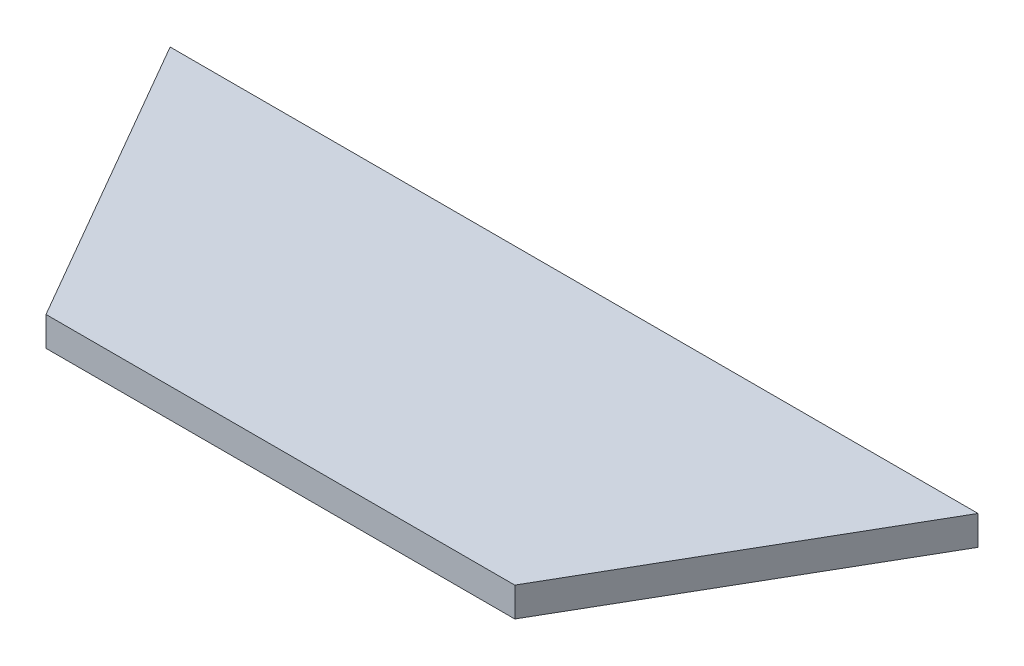
SolidWorks part; units mm, degrees
ref_plane "Спереди" through (0, 0, 0) normal (0, 0, 1) x (1, 0, 0)
ref_plane "Сверху" through (0, 0, 0) normal (0, 1, 0) x (1, 0, 0)
ref_plane "Справа" through (0, 0, 0) normal (1, 0, 0) x (0, 0, -1)
sketch "Эскиз1" plane through (0, 0, 0) normal (0, 1, 0) x (1, 0, 0)
  line L0 (0, 0) -> (79.812, 0)
  line L1 (79.812, 0) -> (108.6795, 50)
  line L2 (108.6795, 50) -> (-28.8675, 50)
  line L3 (-28.8675, 50) -> (0, 0)
  dimension "D1" = 50
extrude "Бобышка-Вытянуть1" add sketch "Эскиз1" along normal blind 5
